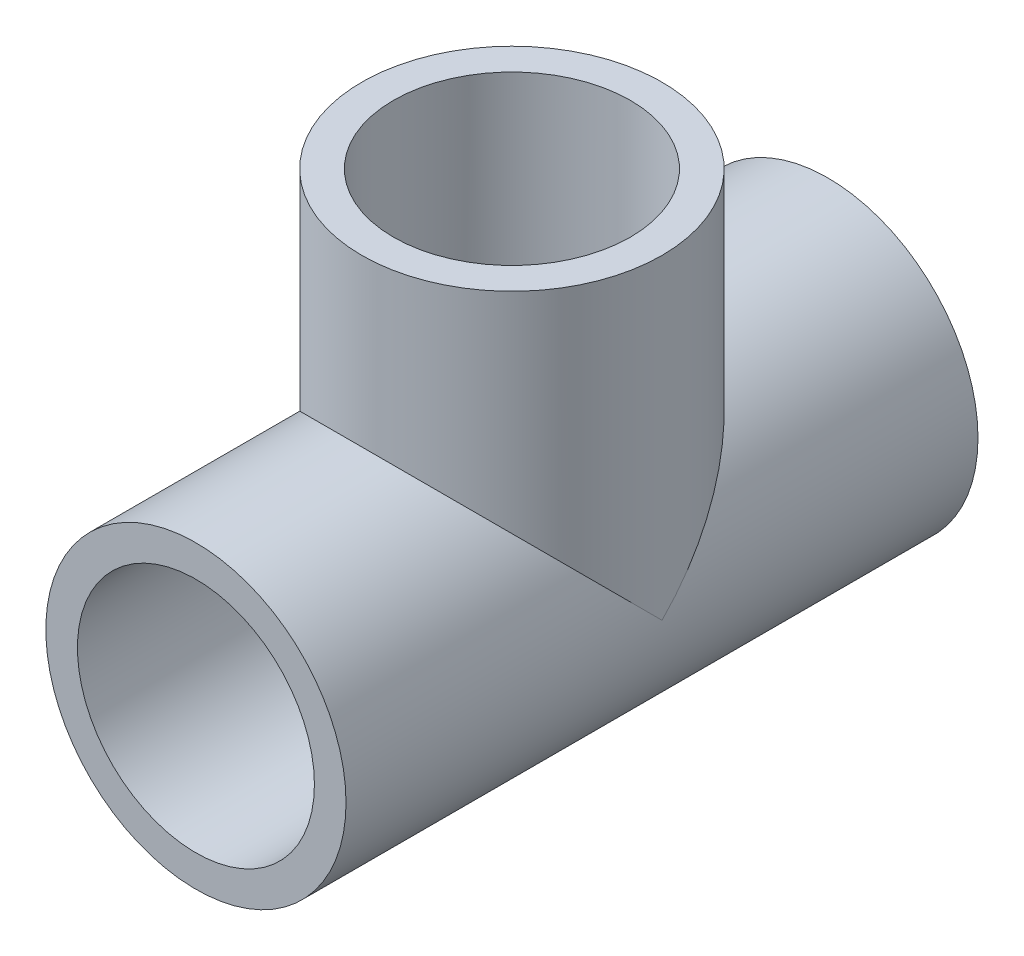
SolidWorks part; units mm, degrees
material "PVC Rigid"
ref_plane "Front Plane" through (0, 0, 0) normal (0, 0, 1) x (1, 0, 0)
ref_plane "Top Plane" through (0, 0, 0) normal (0, 1, 0) x (1, 0, 0)
ref_plane "Right Plane" through (0, 0, 0) normal (1, 0, 0) x (0, 0, -1)
sketch "Sketch1" plane through (0, 0, 0) normal (0, 0, 1) x (1, 0, 0)
  circle A0 centre (0, 0) radius 24.13
  circle A1 centre (0, 0) radius 19.05
  dimension "D1" = 48.26
  dimension "D2" = 38.1
extrude "Boss-Extrude1" add sketch "Sketch1" along normal blind 101.6
sketch "Sketch2" plane through (0, 0, 0) normal (0, 1, 0) x (1, 0, 0)
  line L0 (-24.13, -50.8) -> (24.13, -50.8) construction
  line L1 (-24.13, 0) -> (-24.13, -101.6) construction
  line L2 (24.13, -101.6) -> (24.13, 0) construction
  circle A0 centre (0, -50.8) radius 24.13
  circle A1 centre (0, -50.8) radius 19.05
  point P10 (55.9915, -42.4389)
  point P11 (32.9051, -83.8261)
  point P12 (0, -50.8)
  point P13 (0, -52.2008)
extrude "Boss-Extrude2" add sketch "Sketch2" along normal blind 50.8
sketch "Sketch3" plane through (0, 0, 101.6) normal (0, 0, 1) x (1, 0, 0)
  line L0 (-19.05, 0) -> (19.05, 0) construction
  circle A0 centre (0, 0) radius 19.05
extrude "Cut-Extrude1" cut sketch "Sketch3" against normal through all
